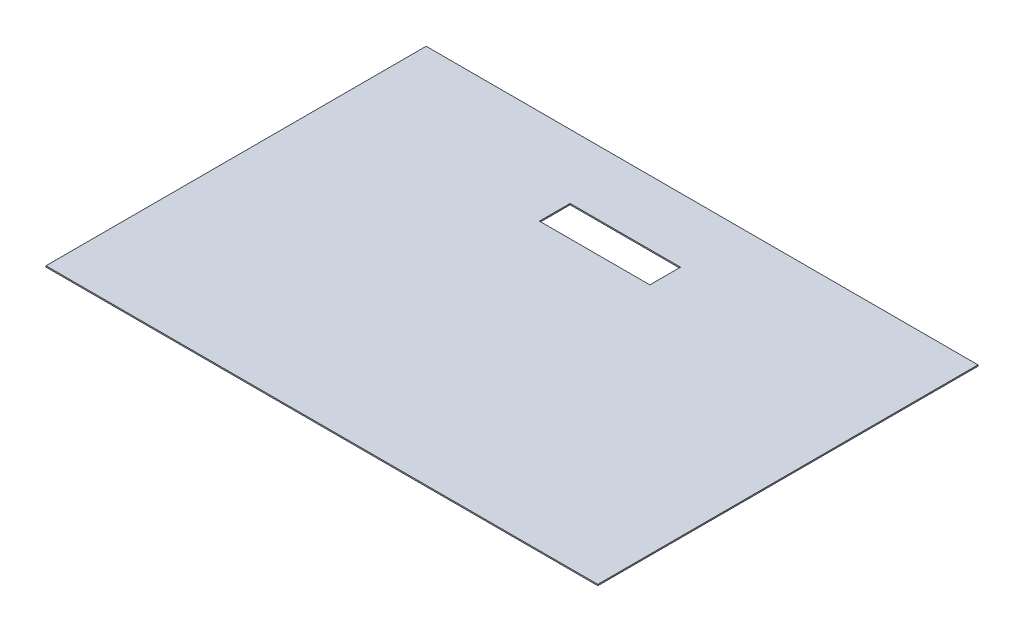
SolidWorks part; units mm, degrees
ref_plane "Front Plane" through (0, 0, 0) normal (0, 0, 1) x (1, 0, 0)
ref_plane "Top Plane" through (0, 0, 0) normal (0, 1, 0) x (1, 0, 0)
ref_plane "Right Plane" through (0, 0, 0) normal (1, 0, 0) x (0, 0, -1)
sketch "Sketch2" plane through (0, 0, 0) normal (0, 1, 0) x (1, 0, 0)
  line L1 (-225, 155) -> (225, 155)
  line L2 (-225, 155) -> (-225, -155)
  line L3 (-225, -155) -> (225, -155)
  line L4 (225, 155) -> (225, -155)
  line L5 (-225, 155) -> (225, -155) construction
  line L6 (-225, -155) -> (225, 155) construction
  line L7 (-55.2911, 102.7) -> (34.7089, 102.7)
  line L8 (-55.2911, 102.7) -> (-55.2911, 77.7)
  line L9 (-55.2911, 77.7) -> (34.7089, 77.7)
  line L10 (34.7089, 102.7) -> (34.7089, 77.7)
  line L11 (-55.2911, 102.7) -> (34.7089, 77.7) construction
  line L12 (-55.2911, 77.7) -> (34.7089, 102.7) construction
  point P0 (0, 0)
  point P6 (-10.2911, 90.2)
  dimension "D1" = 52.3
  dimension "D2" = 90
  dimension "D4" = 25
extrude "Boss-Extrude1" add sketch "Sketch2" along normal blind 1
